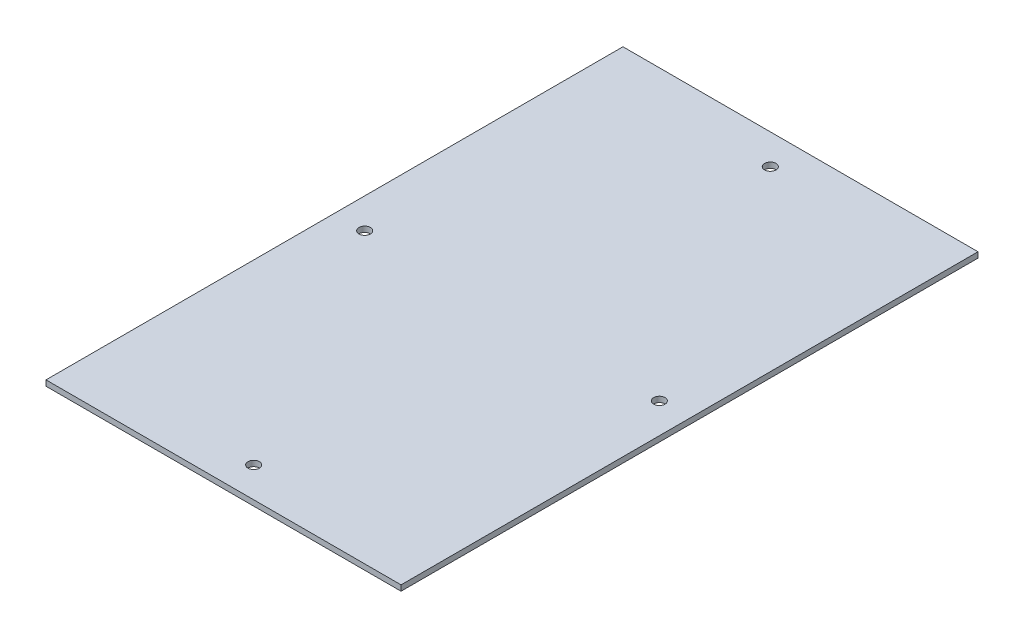
SolidWorks part; units mm, degrees
ref_plane "Front Plane" through (0, 0, 0) normal (0, 0, 1) x (1, 0, 0)
ref_plane "Top Plane" through (0, 0, 0) normal (0, 1, 0) x (1, 0, 0)
ref_plane "Right Plane" through (0, 0, 0) normal (1, 0, 0) x (0, 0, -1)
sketch "Sketch1" plane through (0, 0, 0) normal (0, 1, 0) x (1, 0, 0)
  line L1 (0, 0) -> (203.2, 0)
  line L2 (0, 0) -> (0, -330.2)
  line L3 (0, -330.2) -> (203.2, -330.2)
  line L4 (203.2, 0) -> (203.2, -330.2)
  circle A0 centre (17.272, -165.1) radius 3.2639
  circle A1 centre (101.6, -17.272) radius 3.2639
  circle A2 centre (101.6, -312.928) radius 3.2639
  circle A3 centre (185.928, -165.1) radius 3.2639
  dimension "D3" = 17.272
  dimension "D4" = 6.5278
  dimension "D12" = 6.5278
  dimension "D13" = 6.5278
  dimension "D1" = 330.2
  dimension "D2" = 203.2
  dimension "D5" = 17.272
  dimension "D6" = 165.1
  dimension "D7" = 17.272
  dimension "D8" = 101.6
  dimension "D9" = 101.6
  dimension "D10" = 17.272
  dimension "D11" = 165.1
extrude "Boss-Extrude3" add sketch "Sketch1" along normal blind 3.175
